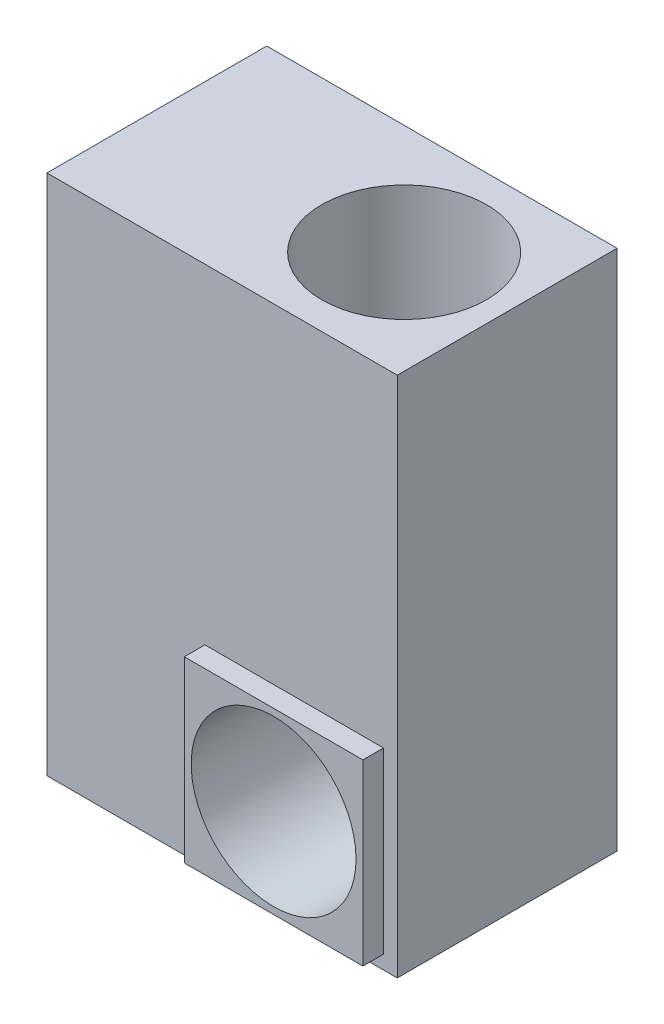
SolidWorks part; units mm, degrees
ref_plane "Front Plane" through (0, 0, 0) normal (0, 0, 1) x (1, 0, 0)
ref_plane "Top Plane" through (0, 0, 0) normal (0, 1, 0) x (1, 0, 0)
ref_plane "Right Plane" through (0, 0, 0) normal (1, 0, 0) x (0, 0, -1)
sketch "Sketch1" plane through (0, 0, 0) normal (0, 0, 1) x (1, 0, 0)
  line L1 (0, 0) -> (-6.375, 0)
  line L2 (0, 0) -> (0, 9.5)
  line L3 (0, 9.5) -> (-6.375, 9.5)
  line L4 (-6.375, 0) -> (-6.375, 9.5)
  dimension "D1" = 9.5
  dimension "D2" = 6.375
extrude "Boss-Extrude1" add sketch "Sketch1" along normal blind 4
scale "Scale1" scale about centroid uniform scaling yes scale factor 25.4
sketch "Sketch3" plane through (0, 0, 52.8) normal (0, 0, 1) x (1, 0, 0)
  line L0 (77.775, -115.9) -> (77.775, 125.4) construction
  line L1 (71.425, -109.55) -> (-11.125, -109.55)
  line L2 (71.425, -109.55) -> (71.425, -27)
  line L3 (71.425, -27) -> (-11.125, -27)
  line L4 (-11.125, -109.55) -> (-11.125, -27)
  line L5 (-84.15, -115.9) -> (77.775, -115.9) construction
  dimension "D1" = 82.55
  dimension "D2" = 6.35
  dimension "D3" = 6.35
extrude "Boss-Extrude2" add sketch "Sketch3" along normal blind 9.525
sketch "Sketch4" plane through (0, 0, 62.325) normal (0, 0, 1) x (1, 0, 0)
  line L0 (-11.125, -27) -> (71.425, -109.55) construction
  circle A0 centre (30.15, -68.275) radius 38.1
  dimension "D1" = 76.2
extrude "Cut-Extrude1" cut sketch "Sketch4" against normal blind 101.6
sketch "Sketch5" plane through (0, 125.4, 0) normal (0, 1, 0) x (1, 0, 0)
  line L0 (77.775, -52.8) -> (77.775, 48.8) construction
  line L1 (77.775, 48.8) -> (-84.15, 48.8) construction
  circle A0 centre (30.15, -2) radius 38.1
  dimension "D1" = 76.2
  dimension "D2" = 47.625
  dimension "D3" = 50.8
extrude "Cut-Extrude2" cut sketch "Sketch5" against normal blind 101.6
